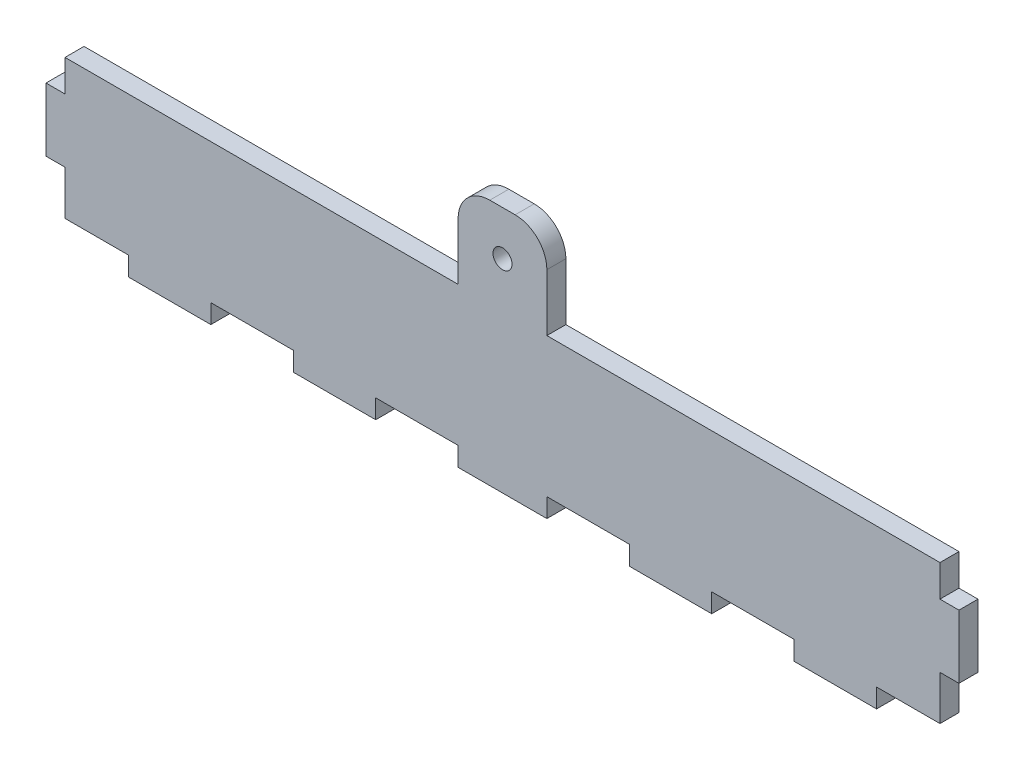
SolidWorks part; units mm, degrees
ref_plane "Front Plane" through (0, 0, 0) normal (0, 0, 1) x (1, 0, 0)
ref_plane "Top Plane" through (0, 0, 0) normal (0, 1, 0) x (1, 0, 0)
ref_plane "Right Plane" through (0, 0, 0) normal (1, 0, 0) x (0, 0, -1)
sketch "Sketch1" plane through (0, 0, 0) normal (0, 0, 1) x (1, 0, 0)
  line L0 (0, 17) -> (0, 22)
  line L1 (0, 0) -> (10, 0)
  line L2 (0, 0) -> (0, 7)
  line L3 (0, 22) -> (62, 22)
  line L4 (138, 0) -> (138, 7)
  line L5 (0, 17) -> (-3, 17)
  line L6 (138, 17) -> (138, 22)
  line L7 (0, 7) -> (-3, 7)
  line L8 (-3, 17) -> (-3, 7)
  line L9 (138, 17) -> (141, 17)
  line L10 (23, 0) -> (36, 0)
  line L11 (138, 7) -> (141, 7)
  line L12 (141, 17) -> (141, 7)
  line L13 (76, 22) -> (138, 22)
  line L14 (10, 0) -> (10, -3)
  line L15 (10, -3) -> (23, -3)
  line L16 (23, 0) -> (23, -3)
  line L18 (36, 0) -> (36, -3)
  line L19 (36, -3) -> (49, -3)
  line L20 (49, 0) -> (49, -3)
  line L21 (62, 22) -> (62, 31)
  line L22 (62, 0) -> (62, -3)
  line L23 (62, -3) -> (76, -3)
  line L24 (76, 0) -> (76, -3)
  line L25 (67, 36) -> (71, 36)
  line L26 (89, 0) -> (89, -3)
  line L27 (89, -3) -> (102, -3)
  line L28 (102, 0) -> (102, -3)
  line L29 (76, 22) -> (76, 31)
  line L30 (115, 0) -> (115, -3)
  line L31 (115, -3) -> (128, -3)
  line L32 (128, 0) -> (128, -3)
  line L33 (49, 0) -> (62, 0)
  line L34 (76, 0) -> (89, 0)
  line L35 (102, 0) -> (115, 0)
  line L36 (128, 0) -> (138, 0)
  arc A0 (71, 36) -> (76, 31) centre (71, 31) cw
  arc A1 (62, 31) -> (67, 36) centre (67, 31) cw
  circle A2 centre (69, 29) radius 1.5
  point P39 (76, 36)
  point P42 (62, 36)
  dimension "D20" = 5
  dimension "D21" = 3
  dimension "D1" = 138
  dimension "D2" = 22
  dimension "D3" = 5
  dimension "D4" = 7
  dimension "D5" = 3
  dimension "D6" = 14
  dimension "D7" = 10
  dimension "D8" = 10
  dimension "D9" = 13
  dimension "D10" = 13
  dimension "D11" = 13
  dimension "D12" = 13
  dimension "D13" = 13
  dimension "D14" = 13
  dimension "D15" = 13
  dimension "D16" = 3
  dimension "D17" = 14
  dimension "D18" = 14
  dimension "D19" = 62
  dimension "D22" = 7
  dimension "D23" = 7
extrude "Boss-Extrude1" add sketch "Sketch1" along normal blind 3
